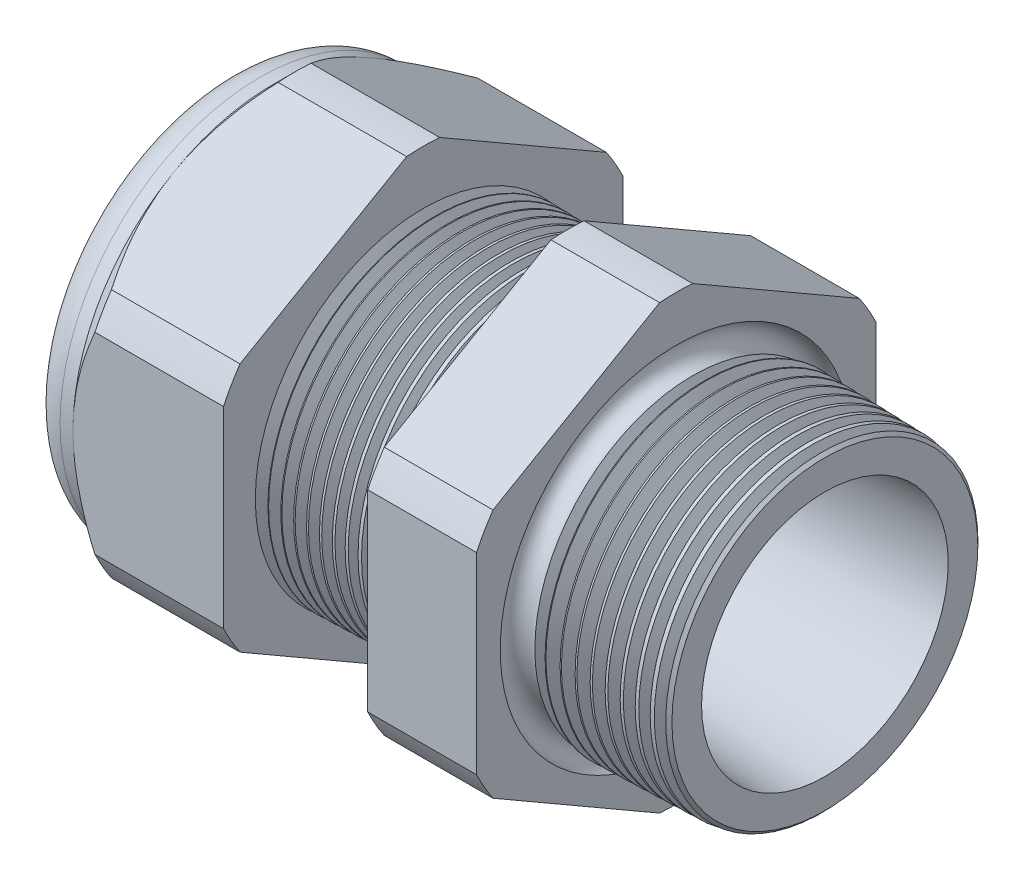
SolidWorks part; units mm, degrees
ref_plane "Front Plane" through (0, 0, 0) normal (0, 0, 1) x (1, 0, 0)
ref_plane "Top Plane" through (0, 0, 0) normal (0, 1, 0) x (1, 0, 0)
ref_plane "Right Plane" through (0, 0, 0) normal (1, 0, 0) x (0, 0, -1)
sketch "Sketch10" plane through (0, 0, 0) normal (0, 0, 1) x (1, 0, 0)
  line L0 (0, 0) -> (-115.3565, 0) construction
  line L1 (-34.798, 5.969) -> (-22.998, 5.969)
  line L2 (1.016, 7.3722) -> (1.016, 9.4042)
  line L3 (-7.874, 9.637) -> (1.016, 9.4042)
  line L4 (-7.874, 23.876) -> (-7.874, 9.637)
  line L5 (-7.874, 23.876) -> (-14.374, 23.876)
  line L6 (-14.374, 23.876) -> (-14.374, 9.8072)
  line L7 (-22.998, 10.033) -> (-14.374, 9.8072)
  line L8 (-22.998, 10.033) -> (-22.998, 23.876)
  line L9 (-22.998, 23.876) -> (-31.998, 23.876)
  line L10 (-31.998, 23.876) -> (-31.998, 11.938)
  line L11 (-31.998, 11.938) -> (-34.798, 11.938)
  line L12 (-34.798, 11.938) -> (-34.798, 5.969)
  line L13 (-22.998, 5.969) -> (1.016, 7.3722)
  dimension "D1" = 35.814
  dimension "D2" = 11.938
  dimension "D3" = 1.5
  dimension "D4" = 2.032
  dimension "A" = 20.066
  dimension "D6" = 23.876
  dimension "D8" = 47.752
  dimension "D9" = 2.8
  dimension "D10" = 9
  dimension "D11" = 6.5
  dimension "D" = 8.89
revolve "Revolve2" add sketch "Sketch10" angle 360 about L0
sketch "Sketch12" plane through (-31.998, 0, 0) normal (-1, 0, 0) x (0, 0, 1)
  line L1 (-0.9882, 13.2143) -> (-10.9498, 7.4629)
  line L2 (-11.938, 5.7513) -> (-11.938, -5.7513)
  line L3 (-10.9498, -7.4629) -> (-0.9882, -13.2143)
  line L4 (0.9882, -13.2143) -> (10.9498, -7.4629)
  line L5 (11.938, -5.7513) -> (11.938, 5.7513)
  line L6 (10.9498, 7.4629) -> (0.9882, 13.2143)
  circle A0 centre (0, 0) radius 11.938 construction
  arc A1 (0.9882, 13.2143) -> (-0.9882, 13.2143) centre (0, 0) ccw
  arc A2 (-10.9498, 7.4629) -> (-11.938, 5.7513) centre (0, 0) ccw
  arc A3 (-11.938, -5.7513) -> (-10.9498, -7.4629) centre (0, 0) ccw
  arc A4 (-0.9882, -13.2143) -> (0.9882, -13.2143) centre (0, 0) ccw
  arc A5 (10.9498, -7.4629) -> (11.938, -5.7513) centre (0, 0) ccw
  arc A6 (11.938, 5.7513) -> (10.9498, 7.4629) centre (0, 0) ccw
  dimension "D2" = 26.5024
  dimension "D1" = 23.876
extrude "Cut-Extrude2" cut sketch "Sketch12" against normal through all flip side to cut
fillet "Fillet4" radius 2.032 1 edges at (-34.798, 0, -11.938)
sketch "Sketch19" plane through (-31.998, 0, 0) normal (-1, 0, 0) x (0, 0, 1)
  line L0 (11.938, 0) -> (11.938, 5.7513) construction
  circle A0 centre (0, 0) radius 11.938
extrude "Cut-Extrude3" cut sketch "Sketch19" against normal blind 2 draft 45 flip side to cut
chamfer "Chamfer1" distance 0.254 angle 45 1 edges at (1.016, 0, -9.4042)
sketch "Sketch21" plane through (-34.798, 0, 0) normal (-1, 0, 0) x (0, 0, 1)
  circle A0 centre (0, 0) radius 5.969
  circle A2 centre (0, 0) radius 5.969 construction
extrude "plug" add sketch "Sketch21" against normal blind 6.35 separate body
sketch "Sketch22" plane through (-34.798, 0, 0) normal (-1, 0, 0) x (0, 0, 1)
  circle A0 centre (0, 0) radius 5.715
  circle A1 centre (0, 0) radius 5.969 construction
  dimension "D1" = 0.254
extrude "Cut-Extrude4" cut sketch "Sketch22" against normal blind 0.508
sketch "Sketch27" plane through (-34.29, 0, 0) normal (-1, 0, 0) x (0, 0, 1)
  line L0 (-4.3624, 0) -> (4.3624, 0) construction
  circle A0 centre (-4.4399, 0) radius 1.27
  circle A1 centre (0, 0) radius 5.715 construction
  dimension "D1" = 0.0051
  dimension "holedia" = 2.54
extrude "plugholes" cut sketch "Sketch27" against normal through all
pattern_circular "CirPattern1" count 2 over 360 about axis through (0, 0, 0) along (1, 0, 0) of "plugholes"
sketch "Sketch28" [suppressed] plane through (-29.464, 0, 0) normal (-1, 0, 0) x (0, 0, 1)
  circle A0 centre (0, 0) radius 0.762
  dimension "midholedia" = 2.54
extrude "midhole" [suppressed] cut sketch "Sketch28" against normal through all
sketch "Sketch29" plane through (0, 0, 0) normal (0, 0, 1) x (1, 0, 0)
  line L0 (-22.998, 10.033) -> (-22.265, 10.0138)
  line L1 (-14.374, 9.8072) -> (-22.998, 10.033) construction
  line L2 (-22.265, 10.0138) -> (-22.6481, 9.3886)
  line L3 (-22.6481, 9.3886) -> (-22.998, 10.033)
  dimension "D1" = 60
  dimension "D2" = 60
  dimension "D3" = 0.635
revolve "Cut-Revolve1" cut sketch "Sketch29" angle 360 about axis through (0, 0, 0) along (-1, 0, 0)
pattern_linear "LPattern1" count 11 spacing 0.762 along (1, 0, 0) of "Cut-Revolve1"
sketch "Sketch30" plane through (0, 0, 0) normal (0, 0, 1) x (1, 0, 0)
  line L0 (-7.874, 9.637) -> (-6.9944, 9.6139)
  line L1 (-7.874, 13.2143) -> (-7.874, 7.4629) construction
  line L2 (0.7621, 9.4108) -> (-7.874, 9.637) construction
  line L3 (-6.9944, 9.6139) -> (-7.4542, 8.8637)
  line L4 (-7.4542, 8.8637) -> (-7.874, 9.637)
  dimension "D1" = 60
  dimension "D2" = 60
  dimension "D3" = 0.762
revolve "Cut-Revolve2" cut sketch "Sketch30" angle 360 about axis through (0, 0, 0) along (-1, 0, 0)
pattern_linear "LPattern2" count 10 spacing 0.889 along (1, 0, 0) of "Cut-Revolve2"
sketch "Sketch31" [suppressed] plane through (-38.354, 0, 0) normal (-1, 0, 0) x (0, 0, 1)
  line L0 (-1.905, 1.905) -> (1.905, 1.905)
  line L1 (-1.905, -1.905) -> (1.905, -1.905)
  circle A0 centre (0, 0) radius 1.905 construction
  arc A1 (-1.905, 1.905) -> (-1.905, -1.905) centre (-1.905, 0) ccw
  arc A2 (1.905, 1.905) -> (1.905, -1.905) centre (1.905, 0) cw
extrude "Cut-Extrude5" [suppressed] cut sketch "Sketch31" against normal through all
sketch "Sketch32" plane through (0, 0, 0) normal (0, 0, 1) x (1, 0, 0)
  line L0 (-7.874, 13.2143) -> (-7.874, 7.4629) construction
  circle A0 centre (-7.747, 9.637) radius 0.889
  dimension "D2" = 1.778
  dimension "D1" = 0.127
revolve "Cut-Revolve3" cut sketch "Sketch32" angle 360 about axis through (0, 0, 0) along (-1, 0, 0)
